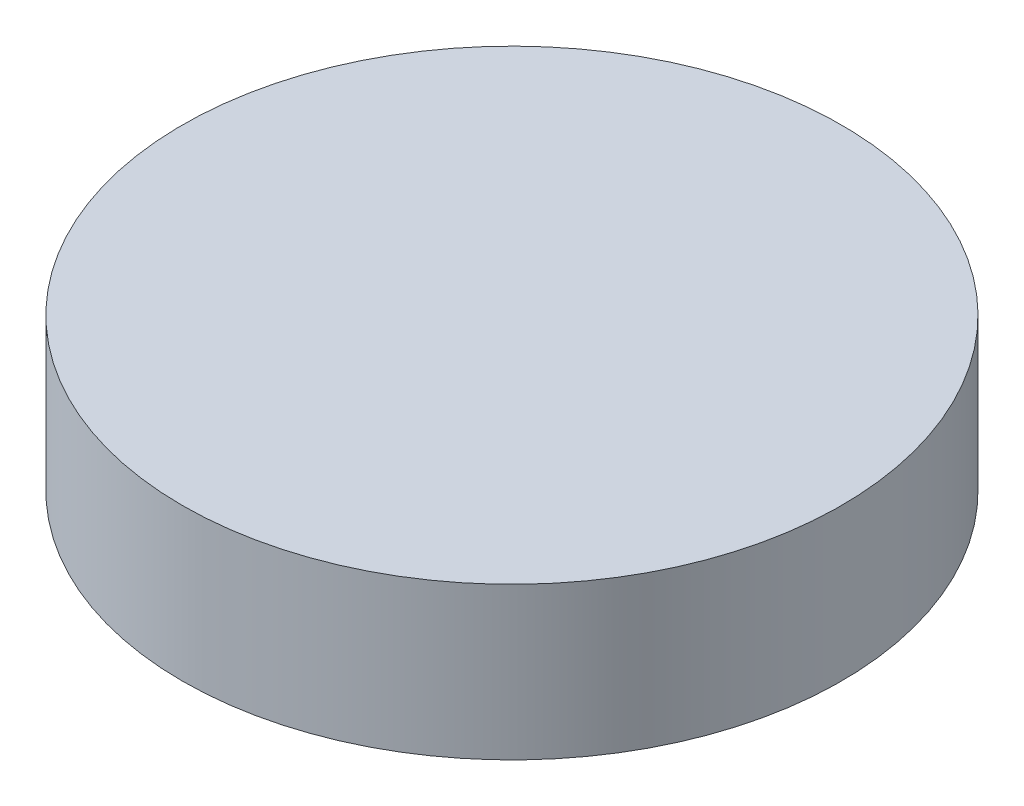
SolidWorks part; units mm, degrees
ref_plane "Front Plane" through (0, 0, 0) normal (0, 0, 1) x (1, 0, 0)
ref_plane "Top Plane" through (0, 0, 0) normal (0, 1, 0) x (1, 0, 0)
ref_plane "Right Plane" through (0, 0, 0) normal (1, 0, 0) x (0, 0, -1)
sketch "Sketch1" plane through (0, 0, 0) normal (0, 1, 0) x (1, 0, 0)
  circle A0 centre (0, 0) radius 65
  dimension "D1" = 130
extrude "Extrude1" add sketch "Sketch1" along normal blind 30
